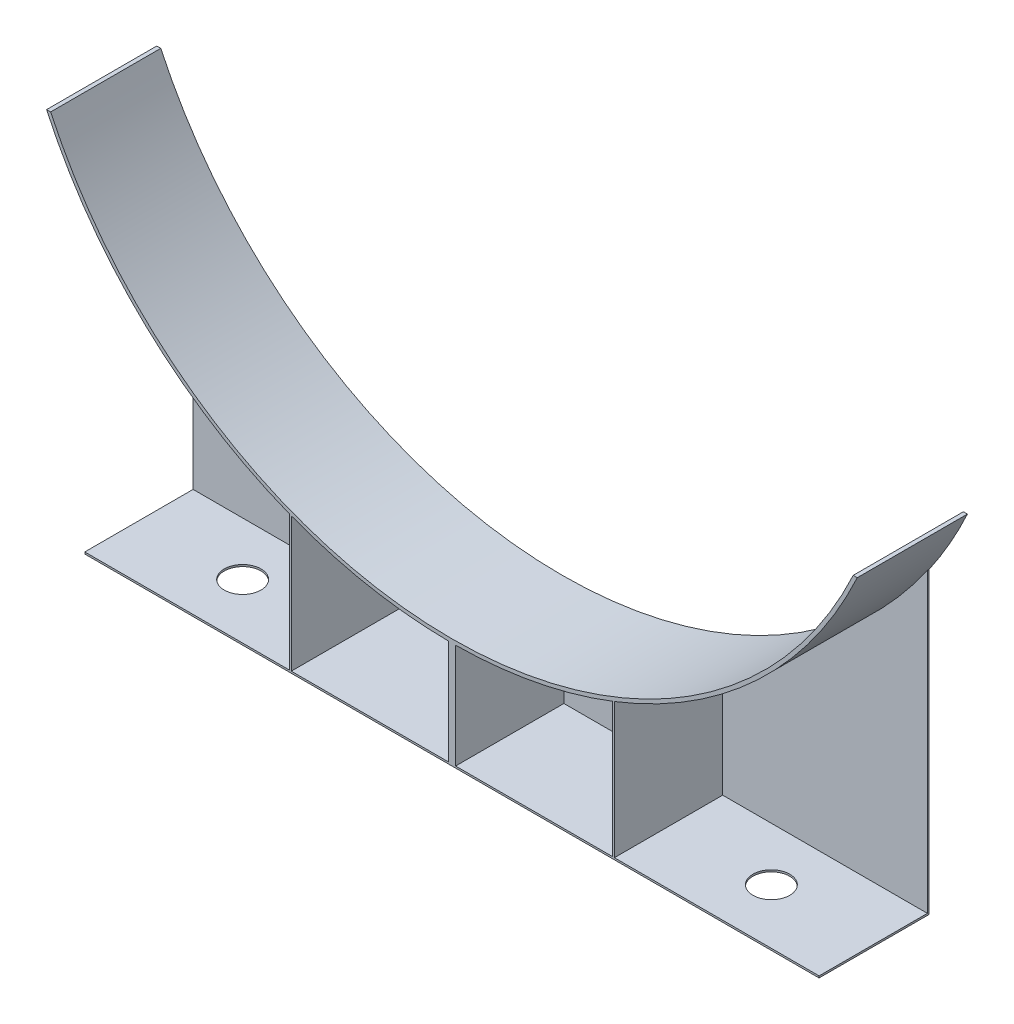
SolidWorks part; units mm, degrees
ref_plane "Front Plane" through (0, 0, 0) normal (0, 0, 1) x (1, 0, 0)
ref_plane "Top Plane" through (0, 0, 0) normal (0, 1, 0) x (1, 0, 0)
ref_plane "Right Plane" through (0, 0, 0) normal (1, 0, 0) x (0, 0, -1)
sketch "Sketch1" plane through (0, 0, 0) normal (0, 0, 1) x (1, 0, 0)
  line L0 (21.8601, -10.1936) -> (22.0806, -10.1936)
  line L1 (-21.8601, -10.1936) -> (-22.0806, -10.1936)
  arc A0 (-21.8601, -10.1936) -> (21.8601, -10.1936) centre (0, 0) ccw
  arc A1 (-22.0806, -10.1936) -> (22.0806, -10.1936) centre (0, 0) ccw
  arc A2 (-22.0414, -10.2781) -> (22.0414, -10.2781) centre (0, 0) ccw construction
  dimension "D1" = 0.2
  dimension "D2" = 24.12
  dimension "D3" = 21.8601
extrude "Boss-Extrude1" add sketch "Sketch1" along normal blind 6 contours A0 L0 A1 L1
sketch "Sketch2" plane through (0, 0, 0) normal (0, 0, 1) x (1, 0, 0)
  line L0 (-0.2, -30.12) -> (0.2, -30.12)
  line L1 (8.75, -30.12) -> (8.85, -30.12)
  line L2 (8.75, -30.12) -> (8.75, -22.6914)
  line L3 (8.85, -30.12) -> (8.85, -22.6526)
  line L4 (-8.75, -30.12) -> (-8.85, -30.12)
  line L5 (-8.75, -30.12) -> (-8.75, -22.6914)
  line L6 (-8.85, -30.12) -> (-8.85, -22.6526)
  line L7 (-0.2, -24.3192) -> (-0.2, -30.12)
  line L8 (-8.75, -30.12) -> (-8.75, -21.3096) construction
  line L9 (-8.85, -30.12) -> (-8.85, -21.3096) construction
  line L10 (0.2, -24.3192) -> (0.2, -30.12)
  line L12 (8.75, -30.12) -> (8.75, -22.4769) construction
  line L13 (8.85, -30.12) -> (8.85, -22.4769) construction
  arc A1 (8.75, -22.6914) -> (8.85, -22.6526) centre (0, 0) ccw
  arc A2 (-0.2, -24.3192) -> (0.2, -24.3192) centre (0, 0) ccw
  arc A3 (-8.85, -22.6526) -> (-8.75, -22.6914) centre (0, 0) ccw
  dimension "D3" = 30.12
  dimension "D1" = 8.75
  dimension "D2" = 0.1
extrude "Boss-Extrude2" add sketch "Sketch2" along normal blind 6
sketch "Sketch3" plane through (0, 0, 0) normal (0, 0, 1) x (1, 0, 0)
  line L1 (-0.2, -30.12) -> (0.2, -30.12) construction
  line L2 (0, -30.12) -> (-20, -30.12)
  line L3 (0, -30.12) -> (20, -30.12)
  line L4 (-20, -30.12) -> (-20, -13.837)
  line L5 (20, -30.12) -> (20, -13.837)
  arc A0 (-20, -13.837) -> (20, -13.837) centre (0, 0) ccw
  dimension "D1" = 24.32
  dimension "D2" = 20
extrude "Boss-Extrude3" add sketch "Sketch3" along normal blind 0.1
ref_plane "Plane1" through (0, -30.12, 0) normal (0, -1, 0) x (-1, 0, 0)
sketch "Sketch4" plane through (0, -30.12, 0) normal (0, -1, 0) x (-1, 0, 0)
  line L0 (-20, 0) -> (-20, -6)
  line L1 (-10.9595, 0) -> (10.9595, 0) construction
  line L2 (-20, -0.1) -> (-20, 0) construction
  line L3 (-20, -6) -> (20, -6)
  line L4 (-20, 0) -> (20, 0)
  line L5 (20, 0) -> (20, -6)
  line L6 (20, -0.1) -> (20, 0) construction
  dimension "D1" = 6
extrude "Boss-Extrude4" add sketch "Sketch4" against normal blind 0.1
sketch "Sketch7" plane through (0, -30.12, 0) normal (0, -1, 0) x (-1, 0, 0)
  circle A0 centre (-14.4, -3) radius 1
  circle A1 centre (14.4, -3) radius 1
  dimension "D1" = 2
  dimension "D2" = 14.4
  dimension "D3" = 14.4
  dimension "D4" = 3
extrude "Cut-Extrude1" cut sketch "Sketch7" against normal blind 1.1
scale "Scale1" scale about centroid uniform scaling yes scale factor 25.4
